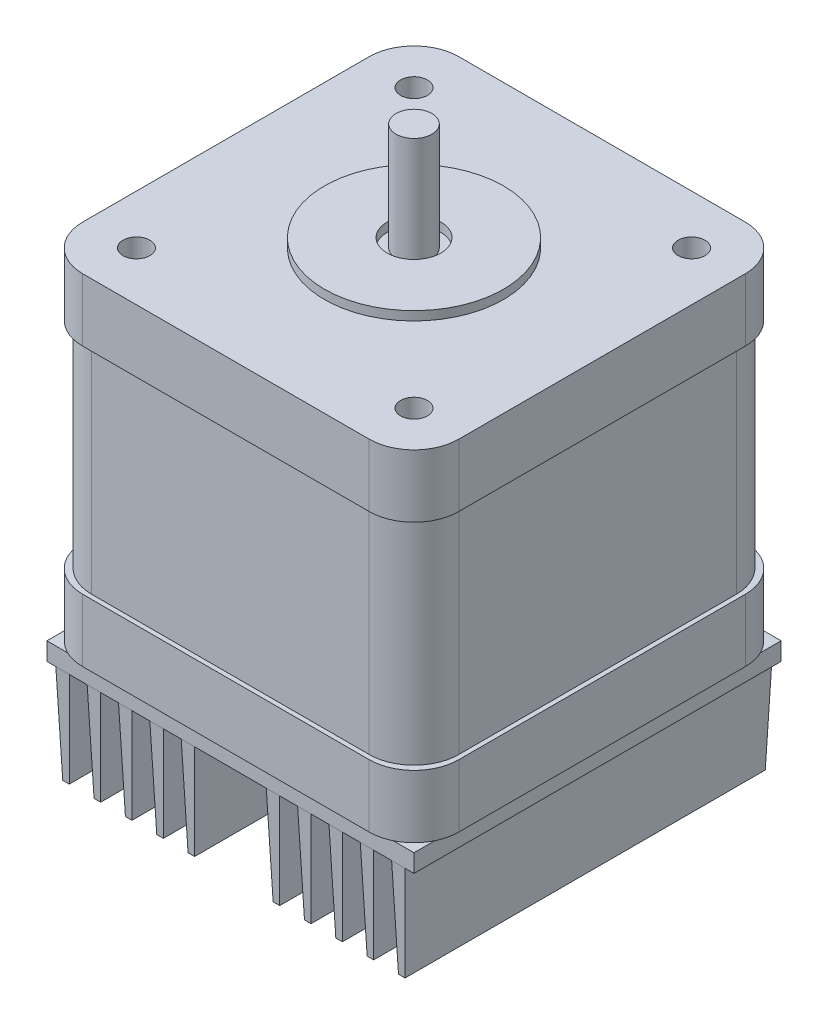
SolidWorks part; units mm, degrees
ref_plane "Front Plane" through (0, 0, 0) normal (0, 0, 1) x (1, 0, 0)
ref_plane "Top Plane" through (0, 0, 0) normal (0, 1, 0) x (1, 0, 0)
ref_plane "Right Plane" through (0, 0, 0) normal (1, 0, 0) x (0, 0, -1)
sketch "Sketch1" plane through (0, 0, 0) normal (0, 1, 0) x (1, 0, 0)
  line L1 (21, 21) -> (-21, 21)
  line L2 (21, 21) -> (21, -21)
  line L3 (21, -21) -> (-21, -21)
  line L4 (-21, 21) -> (-21, -21)
extrude "Extrude1" add sketch "Sketch1" along normal blind 7
fillet "Fillet1" radius 5 4 edges at (21, 3.5, -21) (-21, 3.5, -21) (-21, 3.5, 21) (21, 3.5, 21)
sketch "Sketch2" plane through (0, 7, 0) normal (0, 1, 0) x (1, 0, 0)
  line L1 (-20.5, 20.5) -> (20.5, 20.5)
  line L2 (-20.5, 20.5) -> (-20.5, -20.5)
  line L3 (-20.5, -20.5) -> (20.5, -20.5)
  line L4 (20.5, 20.5) -> (20.5, -20.5)
extrude "Extrude2" add sketch "Sketch2" along normal blind 24 separate body
fillet "Fillet3" radius 5 4 edges at (20.5, 19, 20.5) (20.5, 19, -20.5) (-20.5, 19, -20.5) (-20.5, 19, 20.5)
sketch "Sketch3" plane through (0, 31, 0) normal (0, 1, 0) x (-1, 0, 0)
  line L1 (-21, -21) -> (21, -21)
  line L2 (-21, -21) -> (-21, 21)
  line L3 (-21, 21) -> (21, 21)
  line L4 (21, -21) -> (21, 21)
extrude "Extrude3" add sketch "Sketch3" along normal blind 7 separate body
fillet "Fillet4" radius 5 4 edges at (21, 34.5, -21) (21, 34.5, 21) (-21, 34.5, 21) (-21, 34.5, -21)
sketch "Sketch4" plane through (0, 38, 0) normal (0, 1, 0) x (-1, 0, 0)
  circle A0 centre (0, 0) radius 10
extrude "Extrude4" add sketch "Sketch4" along normal blind 1
sketch "Sketch5" plane through (0, 39, 0) normal (0, 1, 0) x (-1, 0, 0)
  circle A0 centre (0, 0) radius 3
extrude "Extrude5" cut sketch "Sketch5" against normal blind 1
sketch "Sketch6" plane through (0, 38, 0) normal (0, 1, 0) x (-1, 0, 0)
  circle A0 centre (0, 0) radius 2
extrude "Extrude7" add sketch "Sketch6" along normal blind 12
sketch "Sketch7" plane through (0, 0, -20.5) normal (0, 0, -1) x (-1, 0, 0)
  line L0 (-15.5, 7) -> (15.5, 7) construction
  line L1 (10, 7) -> (-10, 7)
  line L2 (10, 7) -> (10, 10)
  line L3 (10, 10) -> (-10, 10)
  line L4 (-10, 7) -> (-10, 10)
extrude "Extrude8" add sketch "Sketch7" along normal blind 3
sketch "Sketch8" plane through (0, 38, 0) normal (0, 1, 0) x (1, 0, 0)
  circle A0 centre (15.5, 15.5) radius 1.5
  circle A1 centre (-15.5, 15.5) radius 1.5
  circle A2 centre (-15.5, -15.5) radius 1.5
  circle A3 centre (15.5, -15.5) radius 1.5
extrude "Extrude9" cut sketch "Sketch8" against normal blind 10
sketch "Sketch9" plane through (0, 0, 0) normal (0, -1, 0) x (1, 0, 0)
  line L1 (-20.5, -20.5) -> (20.5, -20.5)
  line L2 (-20.5, -20.5) -> (-20.5, 20.5)
  line L3 (-20.5, 20.5) -> (20.5, 20.5)
  line L4 (20.5, -20.5) -> (20.5, 20.5)
extrude "Extrude11" add sketch "Sketch9" along normal blind 2 separate body
sketch "Sketch10" plane through (0, -2, 0) normal (0, -1, 0) x (1, 0, 0)
  line L0 (20.5, 20.5) -> (-20.5, 20.5) construction
  line L1 (-19.5, 20.5) -> (-18, 20.5)
  line L2 (-19.5, 20.5) -> (-19.5, -20.5)
  line L3 (-19.5, -20.5) -> (-18, -20.5)
  line L4 (-18, 20.5) -> (-18, -20.5)
  line L5 (-20.5, -20.5) -> (20.5, -20.5) construction
  line L7 (-14.5, 20.5) -> (-16, 20.5)
  line L8 (-14.5, 20.5) -> (-14.5, -20.5)
  line L9 (-14.5, -20.5) -> (-16, -20.5)
  line L10 (-16, 20.5) -> (-16, -20.5)
  line L11 (-11, 20.5) -> (-12.5, 20.5)
  line L12 (-11, 20.5) -> (-11, -20.5)
  line L13 (-11, -20.5) -> (-12.5, -20.5)
  line L14 (-12.5, 20.5) -> (-12.5, -20.5)
  line L15 (-9, 20.5) -> (-7.5, 20.5)
  line L16 (-9, 20.5) -> (-9, -20.5)
  line L17 (-9, -20.5) -> (-7.5, -20.5)
  line L18 (-7.5, 20.5) -> (-7.5, -20.5)
  line L19 (-5.5, 20.5) -> (-4, 20.5)
  line L20 (-5.5, 20.5) -> (-5.5, -20.5)
  line L21 (-5.5, -20.5) -> (-4, -20.5)
  line L22 (-4, 20.5) -> (-4, -20.5)
  line L23 (19.5, 20.5) -> (18, 20.5)
  line L24 (19.5, 20.5) -> (19.5, -20.5)
  line L25 (19.5, -20.5) -> (18, -20.5)
  line L26 (18, 20.5) -> (18, -20.5)
  line L27 (16, 20.5) -> (14.5, 20.5)
  line L28 (16, 20.5) -> (16, -20.5)
  line L29 (16, -20.5) -> (14.5, -20.5)
  line L30 (14.5, 20.5) -> (14.5, -20.5)
  line L31 (12.5, 20.5) -> (11, 20.5)
  line L32 (12.5, 20.5) -> (12.5, -20.5)
  line L33 (12.5, -20.5) -> (11, -20.5)
  line L34 (11, 20.5) -> (11, -20.5)
  line L35 (9, 20.5) -> (7.5, 20.5)
  line L36 (9, 20.5) -> (9, -20.5)
  line L37 (9, -20.5) -> (7.5, -20.5)
  line L38 (7.5, 20.5) -> (7.5, -20.5)
  line L39 (5.5, 20.5) -> (4, 20.5)
  line L40 (5.5, 20.5) -> (5.5, -20.5)
  line L41 (5.5, -20.5) -> (4, -20.5)
  line L42 (4, 20.5) -> (4, -20.5)
extrude "Extrude12" add sketch "Sketch10" along normal blind 11 draft 2
